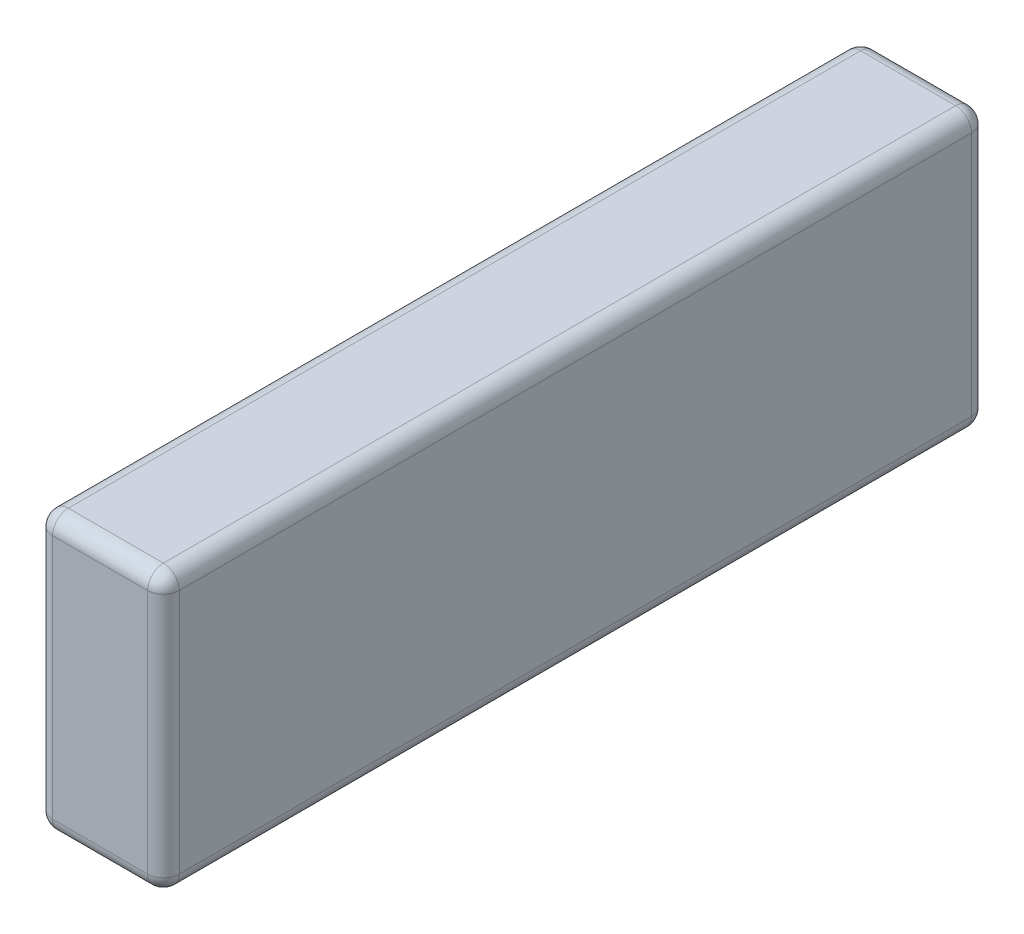
SolidWorks part; units mm, degrees
ref_plane "Front" through (0, 0, 0) normal (0, 0, 1) x (1, 0, 0)
ref_plane "Top" through (0, 0, 0) normal (0, 1, 0) x (1, 0, 0)
ref_plane "Right" through (0, 0, 0) normal (1, 0, 0) x (0, 0, -1)
sketch "Sketch1" plane through (0, 0, 0) normal (0, 1, 0) x (1, 0, 0)
  line L1 (-8, -52) -> (8, -52)
  line L2 (-8, -52) -> (-8, 52)
  line L3 (-8, 52) -> (8, 52)
  line L4 (8, -52) -> (8, 52)
  line L5 (-8, -52) -> (8, 52) construction
  line L6 (-8, 52) -> (8, -52) construction
  point P0 (0, 0)
  dimension "D1" = 16
  dimension "D2" = 104
extrude "Boss-Extrude1" add sketch "Sketch1" along normal blind 35
fillet "Fillet1" radius 2 12 edges at (-8, 17.5, -52) (0, 0, -52) (-8, 0, 0) (8, 17.5, -52) (8, 0, 0) (-8, 17.5, 52) (8, 17.5, 52) (0, 0, 52) (0, 35, 52) (-8, 35, 0) (0, 35, -52) (8, 35, 0)
